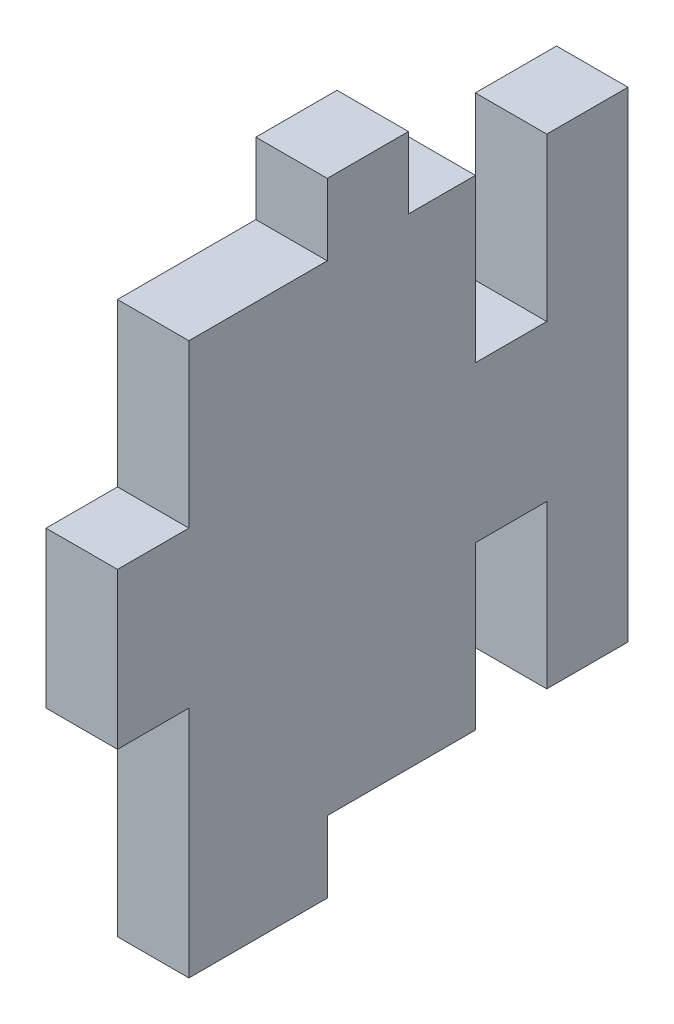
SolidWorks part; units mm, degrees
material "Acrylic (Medium-high impact)"
ref_plane "Front Plane" through (0, 0, 0) normal (0, 0, 1) x (1, 0, 0)
ref_plane "Top Plane" through (0, 0, 0) normal (0, 1, 0) x (1, 0, 0)
ref_plane "Right Plane" through (0, 0, 0) normal (1, 0, 0) x (0, 0, -1)
sketch "Sketch1" plane through (0, 0, 0) normal (1, 0, 0) x (0, 0, -1)
  line L1 (-14, 21.59) -> (14, 21.59)
  line L2 (-14, 21.59) -> (-14, -21.59)
  line L3 (-14, -21.59) -> (14, -21.59)
  line L4 (14, 21.59) -> (14, -21.59)
  line L5 (-14, 21.59) -> (14, -21.59) construction
  line L6 (-14, -21.59) -> (14, 21.59) construction
  line L15 (14, 21.59) -> (8.412, 21.59)
  line L16 (14, 21.59) -> (14, 8.89)
  line L17 (14, 8.89) -> (8.412, 8.89)
  line L18 (8.412, 21.59) -> (8.412, 8.89)
  line L19 (14, -3.302) -> (8.412, -3.302)
  line L20 (14, -3.302) -> (14, -16.002)
  line L21 (14, -16.002) -> (8.412, -16.002)
  line L22 (8.412, -3.302) -> (8.412, -16.002)
  line L35 (-3.175, -21.59) -> (3.175, -21.59)
  line L36 (-3.175, -21.59) -> (-3.175, -16.002)
  line L37 (-3.175, -16.002) -> (3.175, -16.002)
  line L38 (3.175, -21.59) -> (3.175, -16.002)
  line L51 (-3.175, 21.59) -> (3.175, 21.59)
  line L52 (-3.175, 21.59) -> (-3.175, 27.178)
  line L53 (-3.175, 27.178) -> (3.175, 27.178)
  line L54 (3.175, 21.59) -> (3.175, 27.178)
  line L55 (-14, 8.89) -> (-19.588, 8.89)
  line L56 (-14, 8.89) -> (-14, -3.302)
  line L57 (-14, -3.302) -> (-19.588, -3.302)
  line L58 (-19.588, 8.89) -> (-19.588, -3.302)
  line L59 (14, 21.59) -> (20.35, 21.59)
  line L60 (14, 21.59) -> (14, -21.59)
  line L61 (14, -21.59) -> (20.35, -21.59)
  line L62 (20.35, 21.59) -> (20.35, -21.59)
  line L63 (3.175, -16.002) -> (8.412, -16.002)
  line L64 (3.175, -16.002) -> (3.175, -21.59)
  line L65 (3.175, -21.59) -> (8.412, -21.59)
  line L66 (8.412, -16.002) -> (8.412, -21.59)
  line L67 (14, -16.002) -> (20.35, -16.002)
  line L68 (14, -16.002) -> (14, -21.59)
  line L69 (14, -21.59) -> (20.35, -21.59)
  line L70 (20.35, -16.002) -> (20.35, -21.59)
  point P0 (0, 0)
  point P26 (0, 27.178)
  point P27 (0, -16.002)
  dimension "D1" = 28
  dimension "D2" = 43.18
  dimension "D3" = 12.7
  dimension "D4" = 5.588
  dimension "D5" = 12.7
  dimension "D6" = 5.588
  dimension "D7" = 5.588
  dimension "D8" = 6.35
  dimension "D9" = 12.192
  dimension "D10" = 5.588
  dimension "D11" = 6.35
  dimension "D12" = 6.35
extrude "Boss-Extrude1" add sketch "Sketch1" along normal blind 5.588
